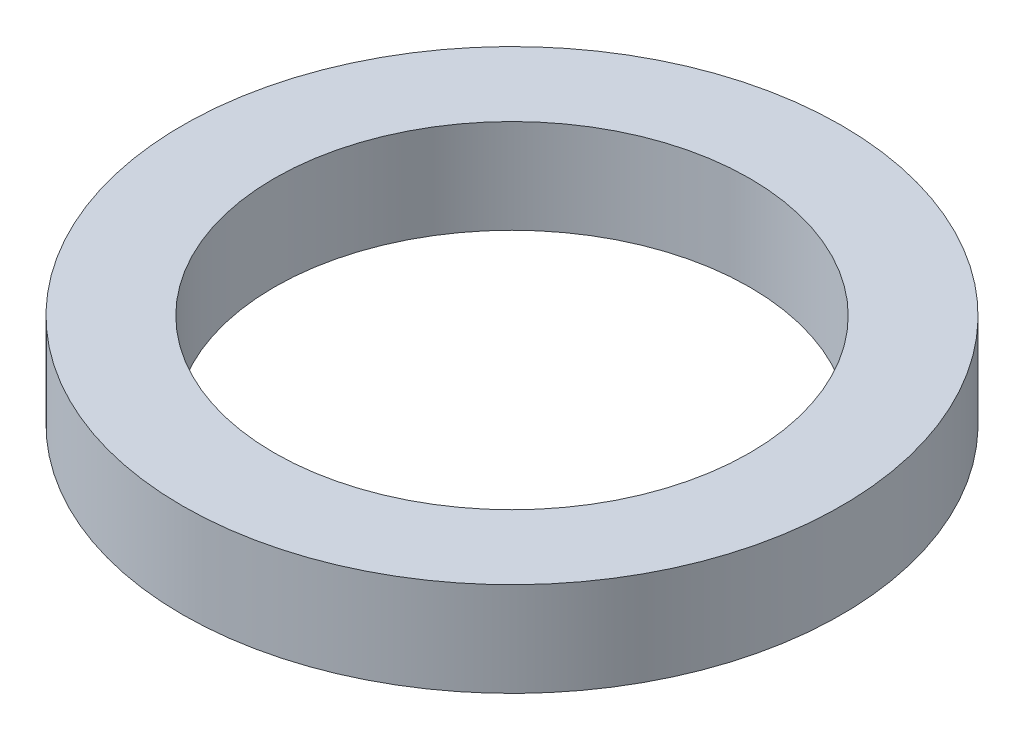
SolidWorks part; units mm, degrees
ref_plane "Front Plane" through (0, 0, 0) normal (0, 0, 1) x (1, 0, 0)
ref_plane "Top Plane" through (0, 0, 0) normal (0, 1, 0) x (1, 0, 0)
ref_plane "Right Plane" through (0, 0, 0) normal (1, 0, 0) x (0, 0, -1)
sketch "Sketch1" plane through (0, 0, 0) normal (0, 1, 0) x (1, 0, 0)
  circle A0 centre (0, 0) radius 3.5
  circle A1 centre (0, 0) radius 2.525
  dimension "D1" = 7
  dimension "D2" = 5.05
extrude "Boss-Extrude1" add sketch "Sketch1" along normal blind 1
